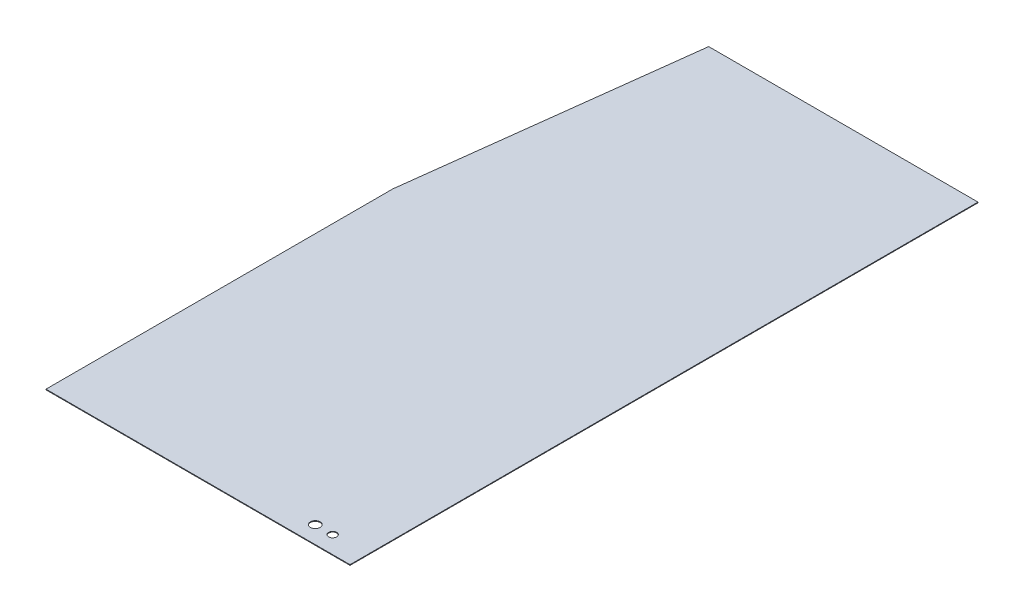
SolidWorks part; units mm, degrees
ref_plane "Alzado" through (0, 0, 0) normal (0, 0, 1) x (1, 0, 0)
ref_plane "Planta" through (0, 0, 0) normal (0, 1, 0) x (1, 0, 0)
ref_plane "Vista lateral" through (0, 0, 0) normal (1, 0, 0) x (0, 0, -1)
sketch "Croquis2" plane through (0, 0, 0) normal (0, 1, 0) x (1, 0, 0)
  line L0 (438.1, 0) -> (-438.1, 0)
  line L1 (-438.1, 0) -> (-438.1, 1000)
  line L2 (-438.1, 1000) -> (-338.1, 1810)
  line L3 (-338.1, 1810) -> (438.1, 1810)
  line L4 (438.1, 1810) -> (438.1, 0)
  line L5 (-438.1, 1000) -> (-438.1, 1810) construction
  line L6 (-438.1, 1810) -> (-338.1, 1810) construction
  dimension "D1" = 876.2
  dimension "D2" = 1000
  dimension "D3" = 1810
  dimension "D4" = 100
  dimension "D5" = 172.962
extrude "Saliente-Extruir1" add sketch "Croquis2" along normal blind 1.9
sketch "Croquis3" plane through (0, 1.9, 0) normal (0, 1, 0) x (1, 0, 0)
  line L0 (438.1, 0) -> (438.1, 1810) construction
  line L1 (-438.1, 0) -> (438.1, 0) construction
  circle A0 centre (338.1, 50) radius 11.5
  circle A1 centre (288.1, 50) radius 14
  point P0 (338.1, 50)
  dimension "D3" = 23
  dimension "D5" = 28
  dimension "D1" = 100
  dimension "D2" = 50
  dimension "D4" = 50
extrude "Cortar-Extruir1" cut sketch "Croquis3" against normal through all both
